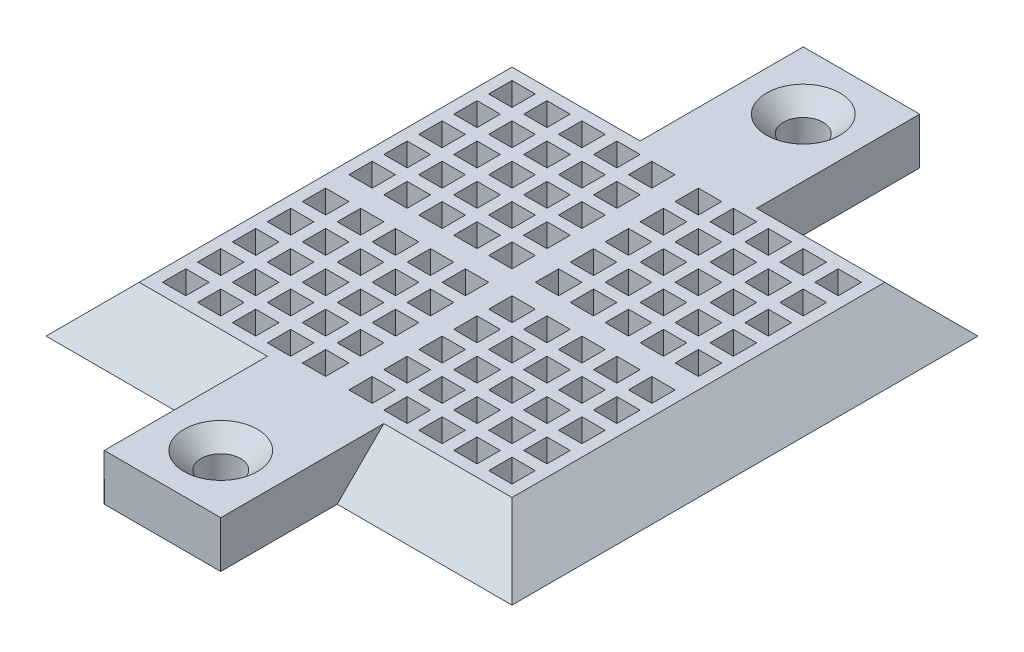
SolidWorks part; units mm, degrees
ref_plane "Спереди" through (0, 0, 0) normal (0, 0, 1) x (1, 0, 0)
ref_plane "Сверху" through (0, 0, 0) normal (0, 1, 0) x (1, 0, 0)
ref_plane "Справа" through (0, 0, 0) normal (1, 0, 0) x (0, 0, -1)
sketch "Эскиз1" plane through (0, 0, 0) normal (0, 1, 0) x (1, 0, 0)
  line L0 (-20, 0) -> (20, 0) construction
  line L1 (20, 20) -> (-20, 20)
  line L2 (20, 20) -> (20, -20)
  line L3 (20, -20) -> (-20, -20)
  line L4 (-20, 20) -> (-20, -20)
  line L5 (20, 20) -> (-20, -20) construction
  line L6 (20, -20) -> (-20, 20) construction
  line L7 (-5, -20) -> (5, -20)
  line L8 (0, -20) -> (0, -30) construction
  line L9 (-5, -20) -> (5, -20)
  line L10 (-5, -20) -> (-5, -30)
  line L11 (-5, -30) -> (5, -30)
  line L12 (5, -20) -> (5, -30)
  line L13 (0, 20) -> (0, 30) construction
  line L14 (-5, 30) -> (5, 30)
  line L15 (5, 20) -> (5, 30)
  line L16 (-5, 20) -> (5, 20)
  line L17 (-5, 20) -> (-5, 30)
  point P0 (0, 0)
  point P11 (0, -20)
  point P15 (0, -25)
  point P16 (0, 25)
  point P23 (0, 0)
  point P24 (0, 0)
  point P25 (0, 0)
  dimension "D1" = 40
  dimension "D3" = 10
extrude "Бобышка-Вытянуть2" add sketch "Эскиз1" along normal blind 4 contours L17 L1 L15 L14 | L1 L4 L3 L2 | L12 L3 L10 L11
draft "Уклон2" type of draft neutral plane draft angle 45 faces to draft 6 face at (-12.5, 2, 20) face at (-20, 2, 0) face at (-12.5, 2, -20) face at (12.5, 2, -20) face at (20, 2, 0) face at (12.5, 2, 20) neutral plane through (0, 0, 0) neutral plane normal (0, -1, 0) reverse direction yes parameters "D1"=45
sketch "Эскиз3" plane through (0, 4, 0) normal (0, 1, 0) x (1, 0, 0)
  line L0 (5, 16) -> (5, 30) construction
  line L1 (-5, 30) -> (5, 30) construction
  line L2 (-5, 30) -> (-5, 20) construction
  line L3 (-5, 20) -> (5, 20) construction
  line L4 (5, 30) -> (5, 20) construction
  line L5 (5, 20) -> (-5, 30) construction
  point P7 (0, 25)
hole_wizard "Зенковка для винта с потайной головкой M31" positions "Трехмерный эскиз2" profile "Эскиз4" countersink size "M3" standard "DIN" end condition up to next
sketch3d "Трехмерный эскиз2"
  point P0 (0, 4, -25)
sketch "Эскиз4" plane through (0, 4, -25) normal (1, 0, 0) x (0, 0, 1)
  line L0 (0, 0) -> (0, 4)
  line L1 (0, 4) -> (1.7, 4)
  line L2 (1.7, 4) -> (1.7, 1.45)
  line L3 (1.7, 1.45) -> (3.15, 0)
  line L5 (3.15, 0) -> (0, 0)
  line L6 (-1.7, 1.45) -> (-3.15, 0) construction
  line L11 (0, -6.35) -> (0, 107.95) construction
  dimension "Диаметр сквозного отверстия" = 3.4
  dimension "Глубина сквозного отверстия" = 4
  dimension "Диаметр передней зенковки" = 6.3
  dimension "Угол передней зенковки" = 90
mirror "Зеркальное отражение1" about plane through (0, 0, 0) normal (0, 0, 1) of "Зенковка для винта с потайной головкой M31"
sketch "Эскиз5" plane through (0, 4, 0) normal (0, 1, 0) x (1, 0, 0)
  line L0 (16, 16) -> (16, -16) construction
  line L1 (15, 15) -> (13, 15)
  line L2 (15, 15) -> (15, 13)
  line L3 (15, 13) -> (13, 13)
  line L4 (13, 15) -> (13, 13)
  line L5 (16, 16) -> (5, 16) construction
  dimension "D1" = 2
  dimension "D2" = 1
  dimension "D3" = 1
extrude "Вырез-Вытянуть1" cut sketch "Эскиз5" against normal up to next (4 mm away)
pattern_linear "Линейный массив1" count 5 spacing 3 along (-1, 0, 0) count 5 spacing 3 along (0, 0, 1) of "Вырез-Вытянуть1"
pattern_linear "Линейный массив2" count 2 spacing 16 along (-1, 0, 0) count 2 spacing 16 along (0, 0, 1) of "Линейный массив1", "Вырез-Вытянуть1"
